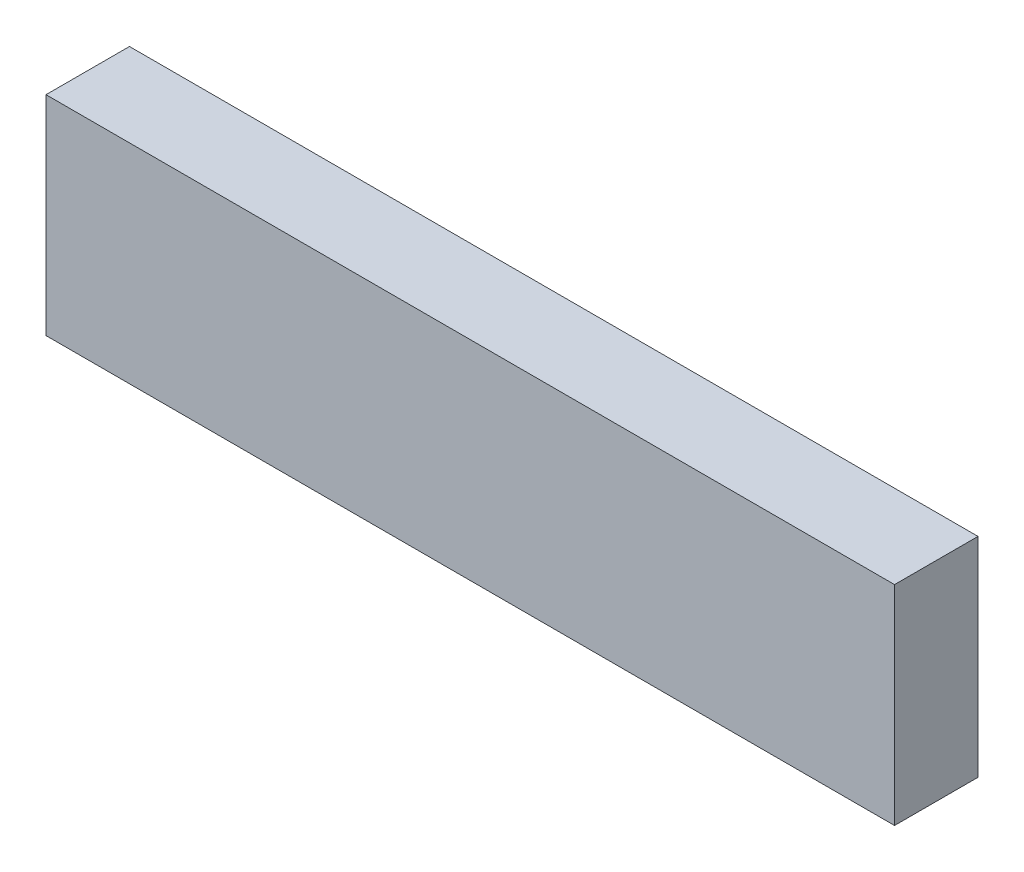
SolidWorks part; units mm, degrees
ref_plane "Front Plane" through (0, 0, 0) normal (0, 0, 1) x (1, 0, 0)
ref_plane "Top Plane" through (0, 0, 0) normal (0, 1, 0) x (1, 0, 0)
ref_plane "Right Plane" through (0, 0, 0) normal (1, 0, 0) x (0, 0, -1)
sketch "Sketch1" plane through (0, 0, 0) normal (1, 0, 0) x (0, 0, -1)
  line L1 (-6, 15) -> (6, 15)
  line L2 (-6, 15) -> (-6, -15)
  line L3 (-6, -15) -> (6, -15)
  line L4 (6, 15) -> (6, -15)
  line L5 (-6, 15) -> (6, -15) construction
  line L6 (-6, -15) -> (6, 15) construction
  point P0 (0, 0)
  dimension "D1" = 12
  dimension "D2" = 30
extrude "Boss-Extrude1" add sketch "Sketch1" along normal mid plane 122
